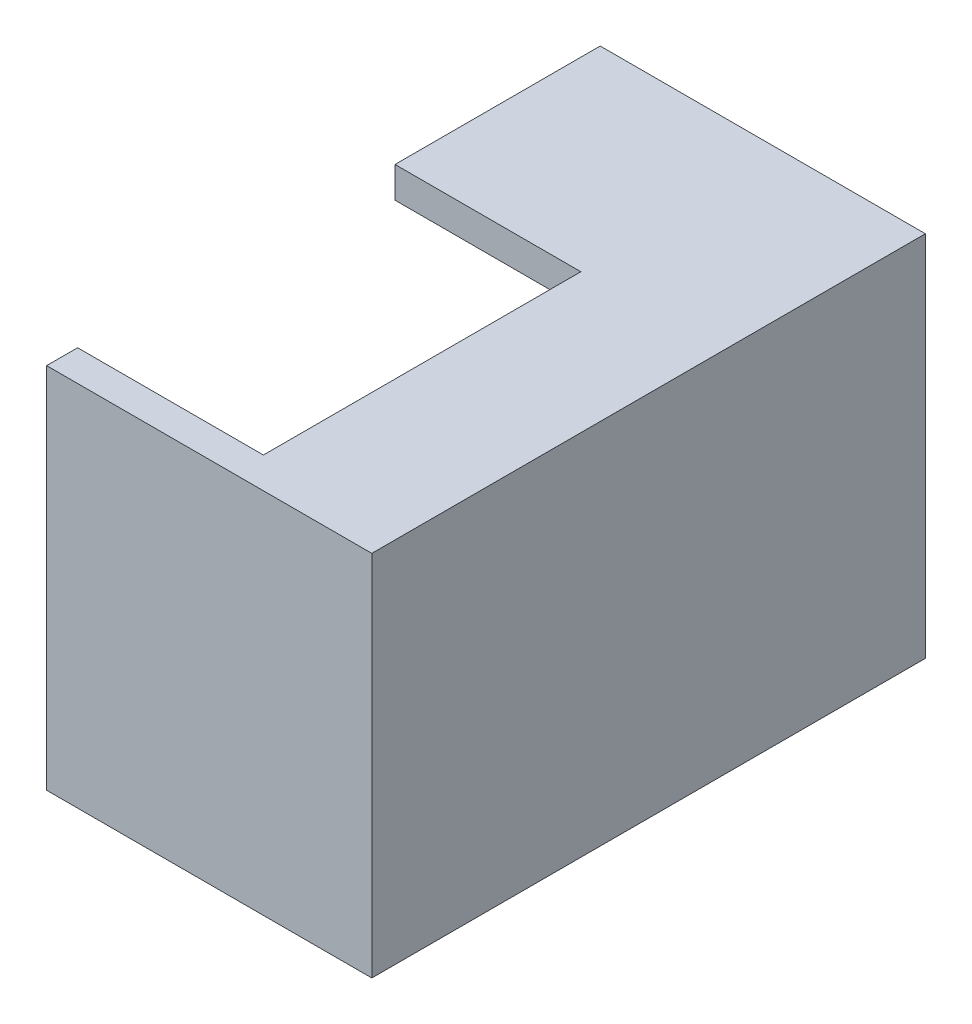
SolidWorks part; units mm, degrees
ref_plane "Front Plane" through (0, 0, 0) normal (0, 0, 1) x (1, 0, 0)
ref_plane "Top Plane" through (0, 0, 0) normal (0, 1, 0) x (1, 0, 0)
ref_plane "Right Plane" through (0, 0, 0) normal (1, 0, 0) x (0, 0, -1)
sketch "Sketch4" plane through (0, 0, 0) normal (1, 0, 0) x (0, 0, -1)
  line L1 (-15.875, 9.875) -> (15.875, 9.875)
  line L2 (-15.875, 9.875) -> (-15.875, -9.875)
  line L3 (-15.875, -9.875) -> (15.875, -9.875)
  line L4 (15.875, 9.875) -> (15.875, -9.875)
  line L5 (-15.875, 9.875) -> (15.875, -9.875) construction
  line L6 (-15.875, -9.875) -> (15.875, 9.875) construction
  point P0 (0, 0)
  dimension "D1" = 31.75
  dimension "D2" = 19.75
extrude "Boss-Extrude1" add sketch "Sketch4" along normal blind 19
shell "Shell1" thickness 2
sketch "Sketch5" plane through (0, 11.875, 0) normal (0, 1, 0) x (1, 0, 0)
  line L0 (0, 4.625) -> (12, 4.625)
  line L1 (0, 17.875) -> (0, -17.875) construction
  line L2 (12, 4.625) -> (12, -15.875)
  line L3 (12, -15.875) -> (0, -15.875)
  line L4 (0, -15.875) -> (0, 4.625)
  line L5 (21, -17.875) -> (0, -17.875) construction
  dimension "D1" = 2
  dimension "D2" = 20.5
  dimension "D3" = 12
extrude "Cut-Extrude1" cut sketch "Sketch5" against normal up to surface (2 mm away) up to face at (9.5, 9.875, 0)
equation "\"terminalRad\"= 3mm"
equation "\"terminalLen\"= 10.5mm"
equation "\"threadlen\"=11"
